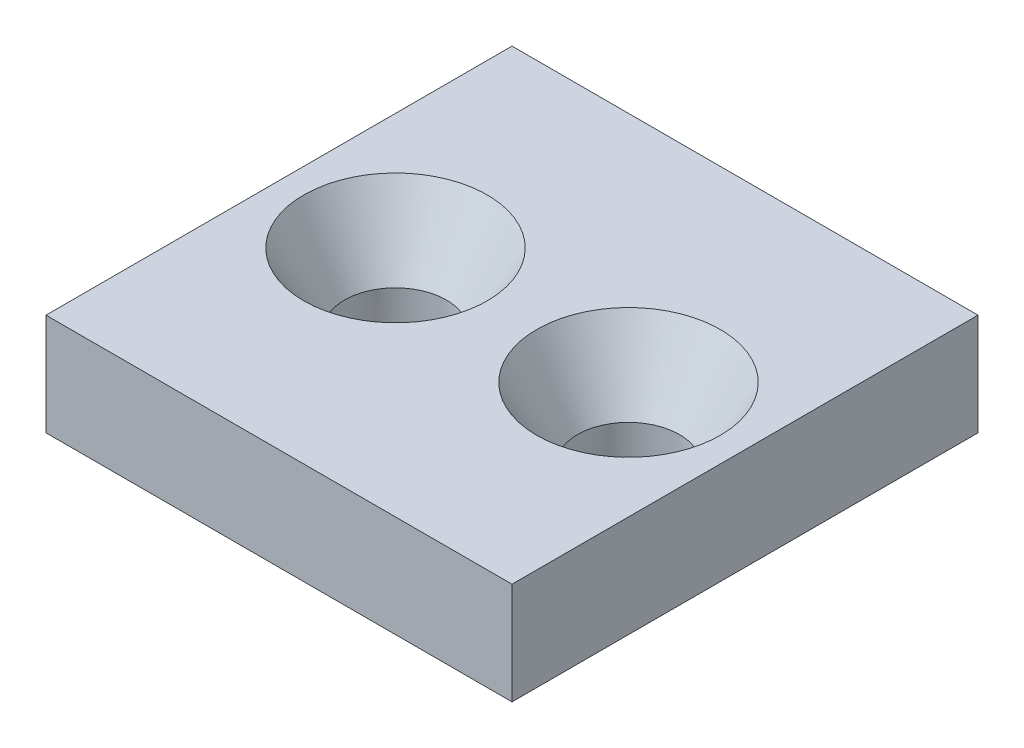
SolidWorks part; units mm, degrees
ref_plane "Front Plane" through (0, 0, 0) normal (0, 0, 1) x (1, 0, 0)
ref_plane "Top Plane" through (0, 0, 0) normal (0, 1, 0) x (1, 0, 0)
ref_plane "Right Plane" through (0, 0, 0) normal (1, 0, 0) x (0, 0, -1)
sketch "Sketch1" plane through (0, 0, 0) normal (0, 1, 0) x (1, 0, 0)
  line L1 (-16, -16) -> (16, -16)
  line L2 (-16, -16) -> (-16, 16)
  line L3 (-16, 16) -> (16, 16)
  line L4 (16, -16) -> (16, 16)
  line L5 (-16, -16) -> (16, 16) construction
  line L6 (-16, 16) -> (16, -16) construction
  point P0 (0, 0)
  dimension "D1" = 32
  dimension "D2" = 32
extrude "Boss-Extrude1" add sketch "Sketch1" along normal blind 7
hole_wizard "CSK for M6 Flat Head Machine Screw1" positions "Sketch2" profile "Sketch3" countersink size "M6" standard "ANSI Metric" end condition up to next
sketch "Sketch2" plane through (0, 7, 0) normal (0, 1, 0) x (1, 0, 0)
  point P0 (-8, 0)
  point P2 (8, 0)
  dimension "D1" = 16
  dimension "D2" = 8
sketch "Sketch3" plane through (-8, 7, 0) normal (1, 0, 0) x (0, 0, 1)
  line L0 (0, 0) -> (0, 7)
  line L1 (0, 7) -> (3.5, 7)
  line L2 (3.5, 7) -> (3.5, 4.8497)
  line L3 (3.5, 4.8497) -> (6.3, 0)
  line L5 (6.3, 0) -> (0, 0)
  line L6 (-3.5, 4.8497) -> (-6.3, 0) construction
  line L11 (0, -6.35) -> (0, 107.95) construction
  dimension "Thru Hole Dia." = 7
  dimension "Thru Hole Depth" = 7
  dimension "Near C'Sink Dia." = 12.6
  dimension "Near C'Sink Angle" = 60
